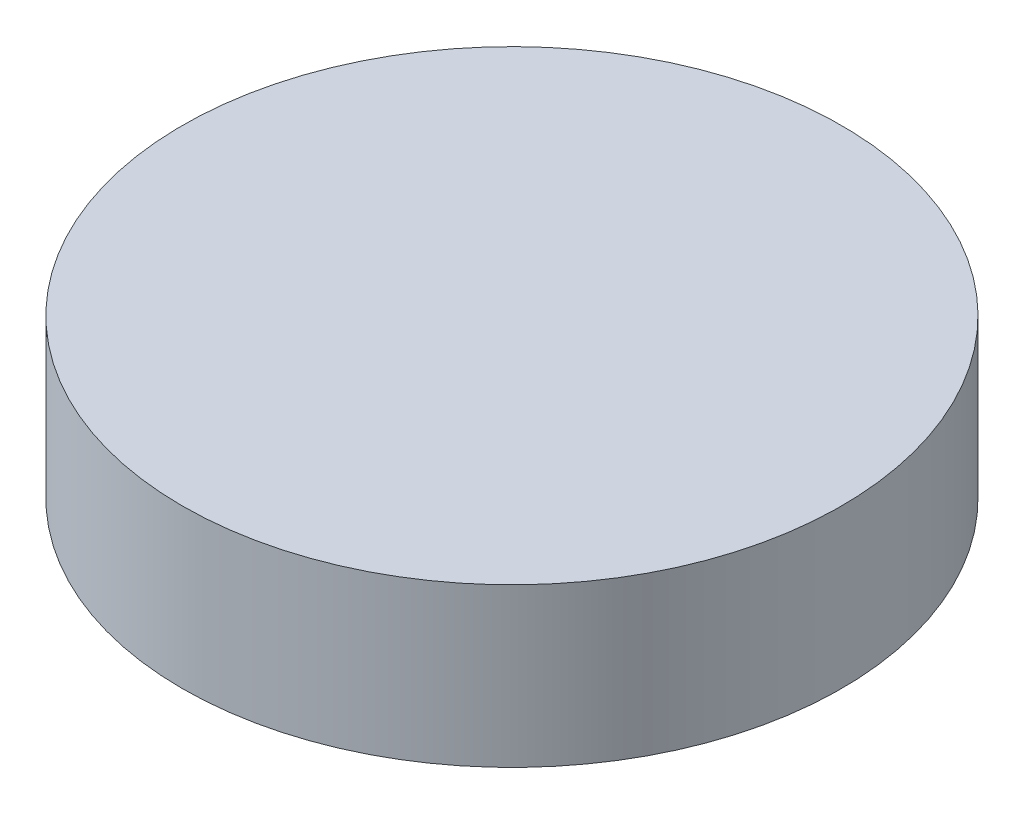
SolidWorks part; units mm, degrees
ref_plane "Alzado" through (0, 0, 0) normal (0, 0, 1) x (1, 0, 0)
ref_plane "Planta" through (0, 0, 0) normal (0, 1, 0) x (1, 0, 0)
ref_plane "Vista lateral" through (0, 0, 0) normal (1, 0, 0) x (0, 0, -1)
sketch "Croquis1" plane through (0, 0, 0) normal (0, 1, 0) x (1, 0, 0)
  line L5 (-25, -12.5) -> (25, 12.5) construction
  line L6 (-25, 12.5) -> (25, -12.5) construction
  circle A5 centre (0, 0) radius 12.5
  point P0 (0, 0)
  dimension "D1" = 25
  dimension "D2" = 50
extrude "Saliente-Extruir1" add sketch "Croquis1" along normal blind 6
